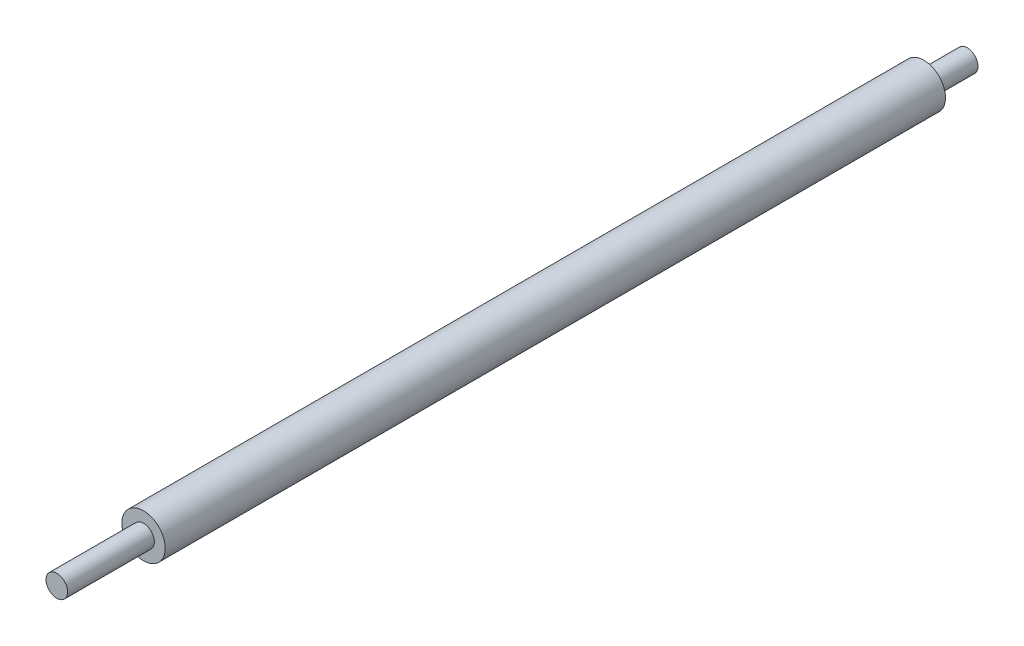
SolidWorks part; units mm, degrees
ref_plane "Front Plane" through (0, 0, 0) normal (0, 0, 1) x (1, 0, 0)
ref_plane "Top Plane" through (0, 0, 0) normal (0, 1, 0) x (1, 0, 0)
ref_plane "Right Plane" through (0, 0, 0) normal (1, 0, 0) x (0, 0, -1)
sketch "Sketch1" plane through (0, 0, 0) normal (0, 0, 1) x (1, 0, 0)
  circle A0 centre (0, 0) radius 5
  dimension "D1" = 10
extrude "Boss-Extrude1" add sketch "Sketch1" along normal blind 180
sketch "Sketch2" plane through (0, 0, 180) normal (0, 0, 1) x (1, 0, 0)
  circle A0 centre (0, 0) radius 2.5
  dimension "D1" = 5
extrude "Boss-Extrude2" add sketch "Sketch2" along normal blind 20
sketch "Sketch3" plane through (0, 0, 0) normal (0, 0, -1) x (-1, 0, 0)
  circle A0 centre (0, 0) radius 2.5
  dimension "D1" = 5
extrude "Boss-Extrude3" add sketch "Sketch3" along normal blind 10
